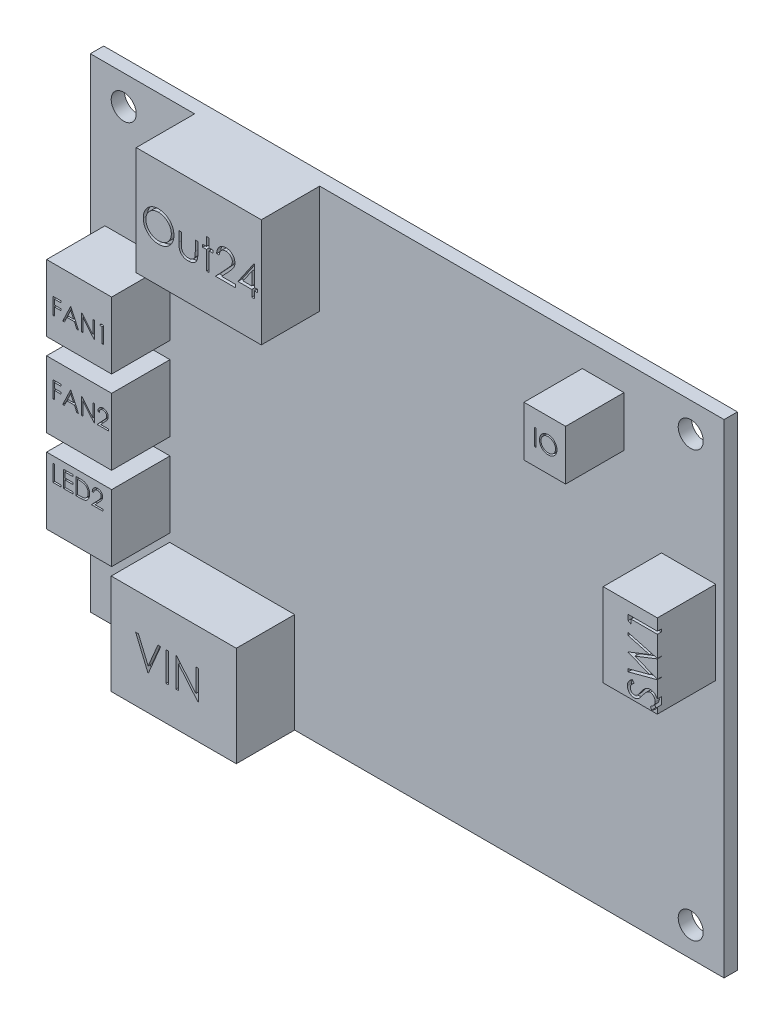
SolidWorks part; units mm, degrees
ref_plane "前视基准面" through (0, 0, 0) normal (0, 0, 1) x (1, 0, 0)
ref_plane "上视基准面" through (0, 0, 0) normal (0, 1, 0) x (1, 0, 0)
ref_plane "右视基准面" through (0, 0, 0) normal (1, 0, 0) x (0, 0, -1)
sketch "草图1" plane through (0, 0, 0) normal (0, 0, 1) x (1, 0, 0)
  line L0 (-66.6253, 0) -> (69.3548, 0) construction
  line L1 (0, 46.7742) -> (0, -50.2481) construction
  line L2 (-26, 0) -> (-26, 29)
  line L3 (-26, 29) -> (50, 29)
  line L4 (50, 29) -> (50, -29)
  line L5 (50, -29) -> (-26, -29)
  line L6 (-26, -29) -> (-26, 0)
  dimension "D1" = 76
  dimension "D2" = 58
  dimension "D3" = 29
  dimension "D4" = 50
extrude "凸台-拉伸1" add sketch "草图1" along normal blind 1.6
sketch "草图4" plane through (0, 0, 1.6) normal (0, 0, 1) x (1, 0, 0)
  line L0 (50, -29) -> (50, 29) construction
  line L1 (50, 29) -> (-26, 29) construction
  line L2 (50, 0) -> (-62.9438, 0) construction
  circle A0 centre (46, 25.5) radius 1.5
  circle A1 centre (46, -25.5) radius 1.5
  circle A2 centre (-22, 25.5) radius 1.5
  circle A3 centre (-22, -25.5) radius 1.5
  dimension "D3" = 3
  dimension "D4" = 68
  dimension "D5" = 3
  dimension "D1" = 4
  dimension "D2" = 3.5
  dimension "D6" = 3.5
extrude "切除-拉伸2" cut sketch "草图4" against normal through all
sketch "草图5" plane through (0, 0, 1.6) normal (0, 0, 1) x (1, 0, 0)
  line L0 (-24.25, 12) -> (-24.25, 4)
  line L1 (-24.25, 4) -> (-16.45, 4)
  line L2 (-16.45, 4) -> (-16.45, 12)
  line L3 (-16.45, 12) -> (-24.25, 12)
  line L4 (50, 29) -> (-26, 29) construction
  line L5 (-26, 29) -> (-26, -29) construction
  line L6 (-24.25, 2) -> (-24.25, -6)
  line L7 (-16.45, 2) -> (-24.25, 2)
  line L8 (-16.45, -6) -> (-16.45, 2)
  line L9 (-24.25, -6) -> (-16.45, -6)
  line L10 (-24.25, -8) -> (-24.25, -16)
  line L11 (-16.45, -8) -> (-24.25, -8)
  line L12 (-16.45, -16) -> (-16.45, -8)
  line L13 (-24.25, -16) -> (-16.45, -16)
  dimension "D1" = 8
  dimension "D2" = 7.8
  dimension "D3" = 17
  dimension "D4" = 1.75
  dimension "D5" = 3
extrude "凸台-拉伸2" add sketch "草图5" along normal blind 7
sketch "草图6" plane through (0, 0, 1.6) normal (0, 0, 1) x (1, 0, 0)
  line L0 (-16.5, -29) -> (-16.5, -17)
  line L1 (-26, -29) -> (50, -29) construction
  line L2 (-16.5, -17) -> (-1.5, -17)
  line L3 (-1.5, -17) -> (-1.5, -29)
  line L4 (-1.5, -29) -> (-16.5, -29)
  line L5 (-26, 29) -> (-26, -29) construction
  dimension "D1" = 9.5
  dimension "D2" = 15
  dimension "D3" = 12
extrude "凸台-拉伸3" add sketch "草图6" along normal blind 7
sketch "草图7" plane through (0, 0, 1.6) normal (0, 0, 1) x (1, 0, 0)
  line L0 (33, 25.8) -> (33, 19.8)
  line L1 (33, 19.8) -> (38, 19.8)
  line L2 (38, 19.8) -> (38, 25.8)
  line L3 (38, 25.8) -> (33, 25.8)
  line L4 (50, -29) -> (50, 29) construction
  line L5 (50, 29) -> (-26, 29) construction
  line L6 (42.5, 11.4) -> (42.5, 1.4)
  line L7 (42.5, 1.4) -> (49, 1.4)
  line L8 (49, 1.4) -> (49, 11.4)
  line L9 (49, 11.4) -> (42.5, 11.4)
  dimension "D1" = 5
  dimension "D2" = 6
  dimension "D3" = 12
  dimension "D4" = 3.2
  dimension "D5" = 10
  dimension "D6" = 6.5
  dimension "D7" = 1
  dimension "D8" = 17.6
extrude "凸台-拉伸4" add sketch "草图7" along normal blind 7
sketch "草图8" plane through (0, 0, 1.6) normal (0, 0, 1) x (1, 0, 0)
  line L0 (-13.5, 28.9725) -> (-13.5, 16)
  line L1 (50, 29) -> (-26, 29) construction
  line L2 (-13.5, 16) -> (1.5, 16)
  line L3 (1.5, 16) -> (1.5, 29)
  line L4 (-13.5, 28.9725) -> (-13.5, 29)
  line L5 (-13.5, 29) -> (1.5, 29)
  line L6 (-26, 29) -> (-26, -29) construction
  dimension "D1" = 15
  dimension "D3" = 12.5
extrude "凸台-拉伸5" add sketch "草图8" along normal blind 7
sketch "草图9" plane through (0, 0, 8.6) normal (0, 0, 1) x (1, 0, 0)
  text T0 "FAN1\r\n\r\nFAN2\r\n\r\nLED2\r\n" font "Century Gothic" height 2
extrude "切除-拉伸3" cut sketch "草图9" against normal blind 0.5
sketch "草图10" plane through (0, 0, 8.6) normal (0, 0, 1) x (1, 0, 0)
  text T0 "Out24"
extrude "切除-拉伸4" cut sketch "草图10" against normal blind 0.5
sketch "草图11" plane through (0, 0, 8.6) normal (0, 0, 1) x (1, 0, 0)
  text T0 "VIN"
extrude "切除-拉伸5" cut sketch "草图11" against normal blind 0.5
sketch "草图12" plane through (0, 0, 8.6) normal (0, 0, 1) x (1, 0, 0)
  text T0 "IO" font "Century Gothic" height 2
extrude "切除-拉伸6" cut sketch "草图12" against normal blind 0.5
sketch "草图13" plane through (0, 0, 8.6) normal (0, 0, 1) x (1, 0, 0)
  text T0 "SW1"
extrude "切除-拉伸7" cut sketch "草图13" against normal blind 0.5
